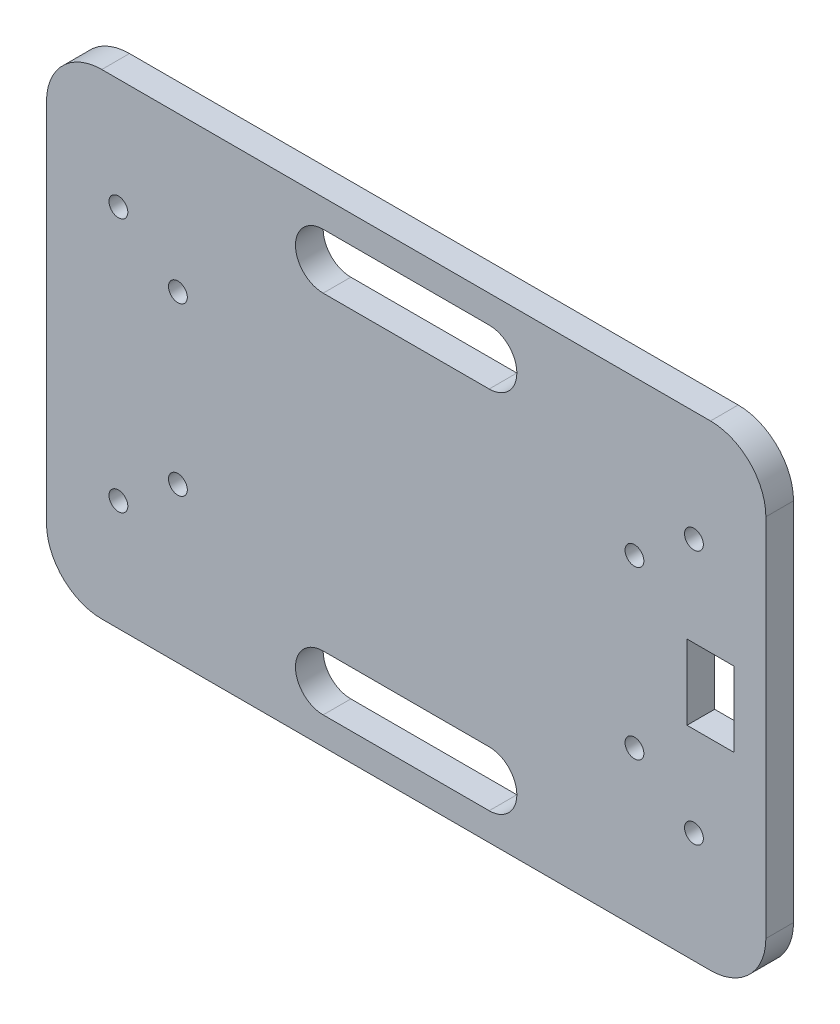
SolidWorks part; units mm, degrees
ref_plane "Front Plane" through (0, 0, 0) normal (0, 0, 1) x (1, 0, 0)
ref_plane "Top Plane" through (0, 0, 0) normal (0, 1, 0) x (1, 0, 0)
ref_plane "Right Plane" through (0, 0, 0) normal (1, 0, 0) x (0, 0, -1)
sketch "Sketch1" plane through (0, 0, 0) normal (0, 0, 1) x (1, 0, 0)
  line L1 (-55, 43) -> (55, 43)
  line L2 (-65, 33) -> (-65, -33)
  line L3 (-55, -43) -> (55, -43)
  line L4 (65, 33) -> (65, -33)
  line L5 (-65, 43) -> (65, -43) construction
  line L6 (-65, -43) -> (65, 43) construction
  arc A0 (-65, 33) -> (-55, 43) centre (-55, 33) cw
  arc A1 (-55, -43) -> (-65, -33) centre (-55, -33) cw
  arc A2 (55, -43) -> (65, -33) centre (55, -33) ccw
  arc A3 (65, 33) -> (55, 43) centre (55, 33) ccw
  point P0 (0, 0)
  point P23 (0, 0)
  dimension "D3" = 10
  dimension "D4" = 10
  dimension "D5" = 10
  dimension "D6" = 10
  dimension "D1" = 130
  dimension "D2" = 86
extrude "Boss-Extrude1" add sketch "Sketch1" along normal blind 5
sketch "Sketch2" plane through (0, 0, 5) normal (0, 0, 1) x (1, 0, 0)
  line L0 (55, 43) -> (-55, 43) construction
  line L1 (-45.5, 19.175) -> (45.5, 19.175)
  line L2 (-45.5, 19.175) -> (-45.5, -19.175)
  line L3 (-45.5, -19.175) -> (45.5, -19.175)
  line L4 (45.5, 19.175) -> (45.5, -19.175)
  line L5 (-45.5, 19.175) -> (45.5, -19.175) construction
  line L6 (-45.5, -19.175) -> (45.5, 19.175) construction
  line L8 (-65, 23) -> (-52, 23) construction
  line L9 (-65, 33) -> (-65, -33) construction
  line L10 (65, -33) -> (65, 33) construction
  line L11 (-55, -43) -> (55, -43) construction
  line L12 (0, 43) -> (0, 33) construction
  line L13 (0, -43) -> (0, -33) construction
  line L14 (-15, -33) -> (15, -33) construction
  line L16 (-15, -28) -> (15, -28)
  line L17 (-15, -38) -> (15, -38)
  line L18 (-15, 33) -> (15, 33) construction
  line L19 (-15, 38) -> (15, 38)
  line L20 (-15, 28) -> (15, 28)
  line L21 (-39.8504, -16.0149) -> (-39.8504, -16.7941) construction
  line L22 (50.75, 6.75) -> (59.25, 6.75)
  line L23 (50.75, 6.75) -> (50.75, -6.75)
  line L24 (50.75, -6.75) -> (59.25, -6.75)
  line L25 (59.25, 6.75) -> (59.25, -6.75)
  line L26 (50.75, 6.75) -> (59.25, -6.75) construction
  line L27 (50.75, -6.75) -> (59.25, 6.75) construction
  circle A0 centre (-52, 23) radius 1.7
  circle A1 centre (-52, -23) radius 1.7
  circle A2 centre (52, -23) radius 1.7
  circle A3 centre (52, 23) radius 1.7
  arc A4 (-15, -28) -> (-15, -38) centre (-15, -33) ccw
  arc A5 (15, -38) -> (15, -28) centre (15, -33) ccw
  arc A6 (-15, 38) -> (-15, 28) centre (-15, 33) ccw
  arc A7 (15, 28) -> (15, 38) centre (15, 33) ccw
  circle A8 centre (-41.25, -15.05) radius 1.7
  circle A9 centre (-41.25, 15.075) radius 1.7
  circle A10 centre (41.25, -15.05) radius 1.7
  circle A11 centre (41.25, 15.075) radius 1.7
  point P0 (0, 0)
  point P31 (0, -33)
  point P37 (0, 33)
  point P51 (55, 0)
  dimension "D3" = 13
  dimension "D5" = 20
  dimension "D11" = 4.25
  dimension "D13" = 30.125
  dimension "D14" = 82.5
  dimension "D15" = 82.5
  dimension "D16" = 10
  dimension "D1" = 91
  dimension "D2" = 38.35
  dimension "D4" = 20
  dimension "D6" = 13
  dimension "D7" = 20
  dimension "D8" = 13
  dimension "D9" = 20
  dimension "D10" = 13
  dimension "D12" = 4.125
  dimension "D17" = 8.5
  dimension "D18" = 13.5
extrude "Cut-Extrude2" cut sketch "Sketch2" against normal blind 5 contours L17 A5 L3 A4 | L1 A7 L19 A6 | A0 | A9 | A8 | A1 | A11 | A10 | A2 | A3 | L23 L22 L25 L24
